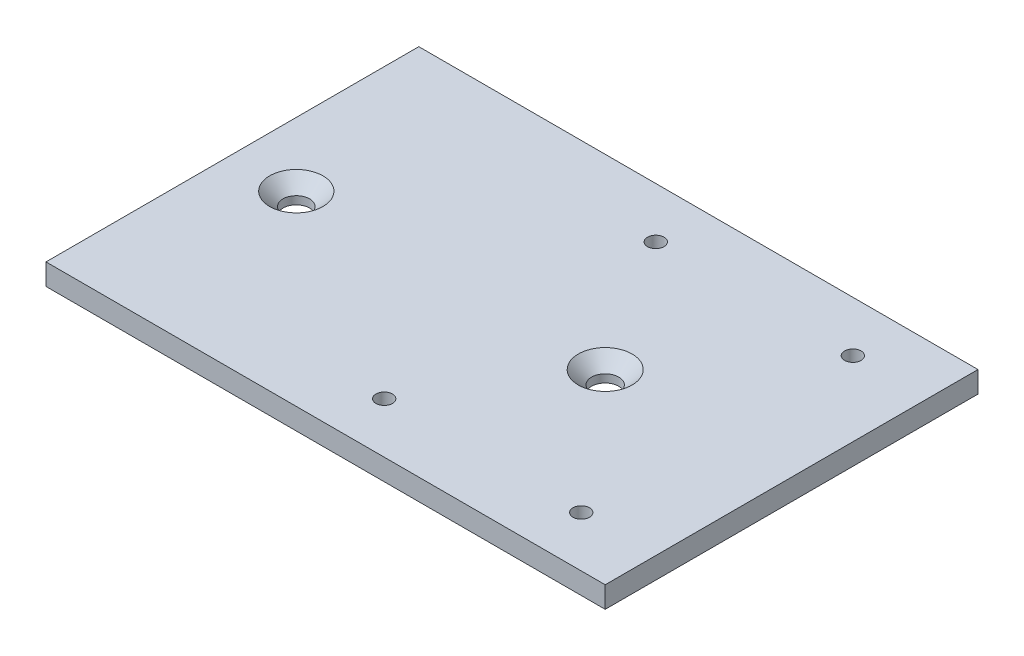
SolidWorks part; units mm, degrees
ref_plane "前视基准面" through (0, 0, 0) normal (0, 0, 1) x (1, 0, 0)
ref_plane "上视基准面" through (0, 0, 0) normal (0, 1, 0) x (1, 0, 0)
ref_plane "右视基准面" through (0, 0, 0) normal (1, 0, 0) x (0, 0, -1)
sketch "草图1" plane through (0, 0, 0) normal (0, 1, 0) x (1, 0, 0)
  line L1 (-18.5, 25.5) -> (18.5, 25.5) construction
  line L2 (-18.5, 25.5) -> (-18.5, -25.5) construction
  line L3 (-18.5, -25.5) -> (18.5, -25.5) construction
  line L4 (18.5, 25.5) -> (18.5, -25.5) construction
  line L5 (-18.5, 25.5) -> (18.5, -25.5) construction
  line L6 (-18.5, -25.5) -> (18.5, 25.5) construction
  line L7 (-22.5, 35) -> (22.5, 35)
  line L8 (-22.5, 35) -> (-22.5, -35)
  line L9 (-22.5, -35) -> (22.5, -35)
  line L10 (22.5, 35) -> (22.5, -35)
  line L11 (-22.5, 35) -> (22.5, -35) construction
  line L12 (-22.5, -35) -> (22.5, 35) construction
  circle A0 centre (18.5, 25.5) radius 1.55
  circle A1 centre (-18.5, 25.5) radius 1.55
  circle A2 centre (-18.5, -25.5) radius 1.55
  circle A3 centre (18.5, -25.5) radius 1.55
  point P0 (0, 0)
  point P6 (0, 0)
  dimension "D5" = 3.1
  dimension "D6" = 3.1
  dimension "D7" = 3.1
  dimension "D8" = 3.1
  dimension "D1" = 37
  dimension "D2" = 51
  dimension "D3" = 45
  dimension "D4" = 70
extrude "凸台-拉伸1" add sketch "草图1" along normal blind 4
ref_plane "基准面1" through (22.5, 0, 0) normal (1, 0, 0) x (0, 0, -1)
ref_plane "基准面2" through (-22.5, 0, 0) normal (-1, 0, 0) x (0, 0, 1)
sketch "草图3" plane through (-22.5, 0, 0) normal (-1, 0, 0) x (0, 0, 1)
  line L1 (-35, 4) -> (35, 4)
  line L2 (-35, 4) -> (-35, 0)
  line L3 (-35, 0) -> (35, 0)
  line L4 (35, 4) -> (35, 0)
extrude "凸台-拉伸3" add sketch "草图3" along normal blind 40
ref_plane "基准面3" through (0, 4, 0) normal (0, 1, 0) x (1, 0, 0)
sketch "草图4" plane through (0, 4, 0) normal (0, 1, 0) x (1, 0, 0)
  line L0 (22.5, 0) -> (-2.5, 0) construction
  line L1 (22.5, -2.2) -> (22.5, 2.2) construction
  circle A0 centre (-2.5, 0) radius 2.55
  dimension "D2" = 5.1
  dimension "D1" = 25
extrude "切除-拉伸1" cut sketch "草图4" against normal blind 6
chamfer "倒角1" distance 2.5 angle 45 1 edges at (-2.5, 4, 2.55)
sketch "草图5" plane through (22.5, 0, 0) normal (1, 0, 0) x (0, 0, -1)
  line L0 (38.5, 4) -> (-38.5, 4) construction
  line L1 (-35, 0) -> (35, 0)
  line L2 (-35, 0) -> (-35, 4)
  line L3 (-35, 4) -> (35, 4)
  line L4 (35, 0) -> (35, 4)
  line L5 (35, 4) -> (35, 0) construction
extrude "凸台-拉伸4" add sketch "草图5" along normal blind 10
ref_plane "基准面4" through (-62.5, 0, 0) normal (-1, 0, 0) x (0, 0, 1)
sketch "草图6" plane through (-62.5, 0, 0) normal (-1, 0, 0) x (0, 0, 1)
  line L0 (35, 0) -> (35, 4) construction
  line L1 (-35, 0) -> (35, 0)
  line L2 (-35, 0) -> (-35, 4)
  line L3 (-35, 4) -> (35, 4)
  line L4 (35, 0) -> (35, 4)
  line L5 (38.5, 4) -> (-38.5, 4) construction
extrude "凸台-拉伸5" add sketch "草图6" along normal blind 10
sketch "草图7" plane through (0, 4, 0) normal (0, 1, 0) x (1, 0, 0)
  line L0 (-72.5, 0) -> (-60.5, 0) construction
  line L1 (-72.5, -35) -> (-72.5, 35) construction
  circle A0 centre (-60.5, 0) radius 2.5
  dimension "D2" = 5
  dimension "D1" = 12
extrude "切除-拉伸2" cut sketch "草图7" against normal blind 10
chamfer "倒角3" distance 2.5 angle 45 1 edges at (-60.5, 4, 2.5)
